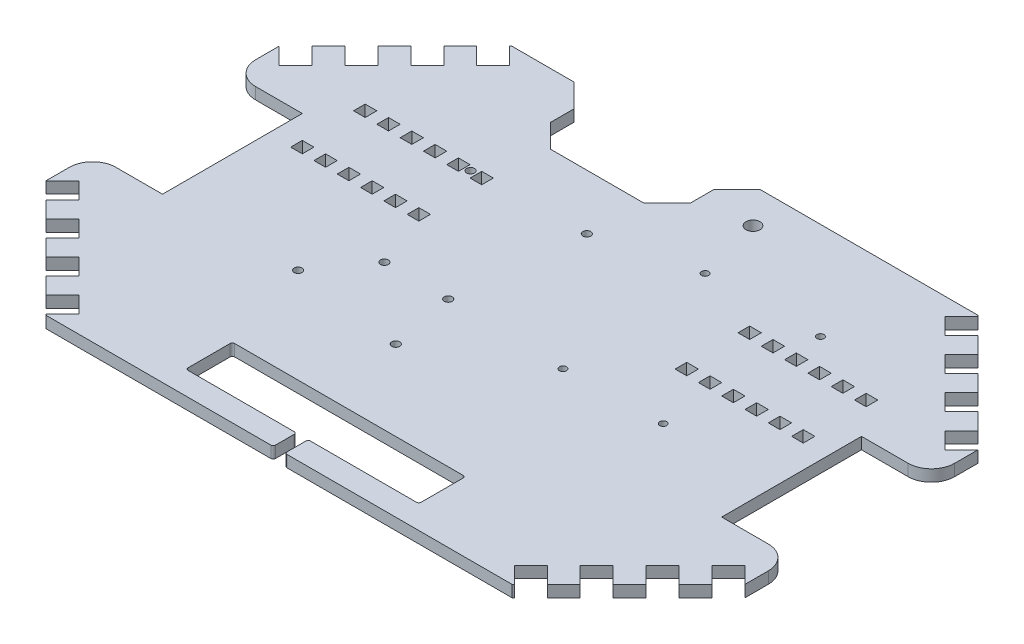
SolidWorks part; units mm, degrees
material "Balsa"
ref_plane "Plan de face" through (0, 0, 0) normal (0, 0, 1) x (1, 0, 0)
ref_plane "Plan de dessus" through (0, 0, 0) normal (0, 1, 0) x (1, 0, 0)
ref_plane "Plan de droite" through (0, 0, 0) normal (1, 0, 0) x (0, 0, -1)
sketch "Esquisse1" plane through (0, 0, 0) normal (0, 1, 0) x (1, 0, 0)
  line L1 (-150, 100) -> (150, 100)
  line L2 (-150, 100) -> (-150, -100)
  line L3 (-150, -100) -> (150, -100)
  line L4 (150, 100) -> (150, -100)
  dimension "D1" = 300
  dimension "D2" = 200
  dimension "D3" = 150
  dimension "D4" = 100
extrude "Boss.-Extru.1" add sketch "Esquisse1" along normal blind 5
sketch "Esquisse2" plane through (0, 5, 0) normal (0, 1, 0) x (1, 0, 0)
  line L0 (-100, 100) -> (-150, 50)
  line L1 (150, 100) -> (-150, 100) construction
  line L2 (-150, 100) -> (-150, -100) construction
  line L3 (-150, 50) -> (-150, 100)
  line L4 (-150, 100) -> (-100, 100)
  line L5 (150, 100) -> (150, 50)
  line L6 (150, -100) -> (150, 100) construction
  line L7 (150, 50) -> (100, 100)
  line L8 (100, 100) -> (150, 100)
  line L9 (150, -100) -> (150, -50)
  line L10 (150, -50) -> (100, -100)
  line L11 (-150, -100) -> (150, -100) construction
  line L12 (100, -100) -> (150, -100)
  line L13 (-100, -100) -> (-150, -100)
  line L14 (-150, -100) -> (-150, -50)
  line L15 (-150, -50) -> (-100, -100)
  dimension "D1" = 50
  dimension "D2" = 50
  dimension "D3" = 50
  dimension "D4" = 50
  dimension "D5" = 50
  dimension "D6" = 50
  dimension "D7" = 50
  dimension "D8" = 50
extrude "Enlèv. mat.-Extru.1" cut sketch "Esquisse2" against normal blind 10
sketch "Esquisse6" plane through (0, 5, 0) normal (0, 1, 0) x (1, 0, 0)
  line L0 (-142.9289, 57.0711) -> (-150, 50)
  line L1 (-142.9289, 57.0711) -> (-135.8579, 50)
  line L2 (-150, 50) -> (-142.9289, 42.9289)
  line L3 (-135.8579, 50) -> (-142.9289, 42.9289)
  line L4 (-150, 50) -> (-100, 100) construction
  dimension "D1" = 10
  dimension "D2" = 10
  dimension "D3" = 0
extrude "Enlèv. mat.-Extru.5" cut sketch "Esquisse6" against normal blind 10
pattern_linear "Répétition linéaire2" count 4 spacing 20 along (0.7071, 0, -0.7071) of "Enlèv. mat.-Extru.5"
mirror "Symétrie1" about plane through (0, 0, 0) normal (0, 0, 1) of "Répétition linéaire2", "Enlèv. mat.-Extru.5"
sketch "Esquisse11" plane through (0, 5, 0) normal (0, 1, 0) x (1, 0, 0)
  line L0 (150, -50) -> (150, 50) construction
  line L1 (150, -7.5) -> (120, -7.5)
  line L2 (150, -7.5) -> (150, 7.5)
  line L3 (150, 7.5) -> (120, 7.5)
  line L4 (120, -7.5) -> (120, 7.5)
  dimension "D1" = 30
  dimension "D2" = 15
  dimension "D3" = 42.5
extrude "Enlèv. mat.-Extru.10" cut sketch "Esquisse11" against normal blind 10
mirror "Symétrie2" about plane through (0, 0, 0) normal (1, 0, 0) of "Enlèv. mat.-Extru.10", "Symétrie1", "Enlèv. mat.-Extru.5", "Répétition linéaire2"
sketch "Esquisse17" plane through (0, 5, 0) normal (0, 1, 0) x (1, 0, 0)
  line L0 (100, 100) -> (-100, 100) construction
  line L1 (-3.4315, 100) -> (-63.4315, 100)
  line L2 (-3.4315, 100) -> (-3.4315, 70)
  line L3 (-3.4315, 70) -> (-63.4315, 70)
  line L4 (-63.4315, 100) -> (-63.4315, 70)
  dimension "D1" = 60
  dimension "D2" = 30
  dimension "D3" = 30
extrude "Enlèv. mat.-Extru.16" cut sketch "Esquisse17" against normal blind 10
chamfer "Chanfrein1" distance 10 angle 45 4 edges at (-63.4315, 2.5, -100) (-63.4315, 2.5, -70) (-3.4315, 2.5, -70) (-3.4315, 2.5, -100)
sketch "Esquisse18" plane through (0, 5, 0) normal (0, 1, 0) x (1, 0, 0)
  line L0 (-150, 50) -> (-150, 7.5) construction
  line L1 (-150, 30) -> (-120, 30)
  line L2 (-150, 30) -> (-150, -30)
  line L3 (-150, -30) -> (-120, -30)
  line L4 (-120, 30) -> (-120, -30)
  line L5 (0, 18.442) -> (0, -22.4339) construction
  line L6 (120, 30) -> (120, -30)
  line L7 (150, -30) -> (120, -30)
  line L8 (150, 30) -> (150, -30)
  line L9 (150, 30) -> (120, 30)
  dimension "D1" = 60
  dimension "D2" = 30
  dimension "D3" = 20
extrude "Enlèv. mat.-Extru.17" cut sketch "Esquisse18" against normal blind 10
sketch "Esquisse20" plane through (0, 0, 0) normal (0, -1, 0) x (1, 0, 0)
  line L0 (-73.4315, -100) -> (-100, -100) construction
  circle A0 centre (18.4315, -85) radius 3
  dimension "D1" = 6
  dimension "D2" = 15
  dimension "D3" = 75
extrude "Enlèv. mat.-Extru.19" cut sketch "Esquisse20" against normal blind 10
sketch "Esquisse21" plane through (0, 0, 0) normal (0, -1, 0) x (1, 0, 0)
  line L1 (110, -42) -> (105, -42)
  line L2 (110, -42) -> (110, -47)
  line L3 (110, -47) -> (105, -47)
  line L4 (105, -42) -> (105, -47)
  line L5 (150, 50) -> (150, 30) construction
  line L6 (95, -42) -> (95, -47)
  line L7 (100, -42) -> (100, -47)
  line L8 (100, -47) -> (95, -47)
  line L9 (100, -42) -> (95, -42)
  line L10 (85, -42) -> (85, -47)
  line L11 (90, -42) -> (90, -47)
  line L12 (90, -47) -> (85, -47)
  line L13 (90, -42) -> (85, -42)
  line L14 (75, -42) -> (75, -47)
  line L15 (80, -42) -> (80, -47)
  line L16 (80, -47) -> (75, -47)
  line L17 (80, -42) -> (75, -42)
  line L18 (65, -42) -> (65, -47)
  line L19 (70, -42) -> (70, -47)
  line L20 (70, -47) -> (65, -47)
  line L21 (70, -42) -> (65, -42)
  line L22 (55, -42) -> (55, -47)
  line L23 (60, -42) -> (60, -47)
  line L24 (60, -47) -> (55, -47)
  line L25 (60, -42) -> (55, -42)
  line L26 (95, -20) -> (100, -20)
  line L27 (105, -20) -> (110, -20)
  line L28 (105, -20) -> (105, -15)
  line L29 (105, -15) -> (110, -15)
  line L30 (110, -20) -> (110, -15)
  line L31 (95, -20) -> (95, -15)
  line L32 (95, -15) -> (100, -15)
  line L33 (100, -20) -> (100, -15)
  line L34 (85, -20) -> (90, -20)
  line L35 (85, -20) -> (85, -15)
  line L36 (85, -15) -> (90, -15)
  line L37 (90, -20) -> (90, -15)
  line L38 (75, -20) -> (80, -20)
  line L39 (75, -20) -> (75, -15)
  line L40 (75, -15) -> (80, -15)
  line L41 (80, -20) -> (80, -15)
  line L42 (65, -20) -> (70, -20)
  line L43 (65, -20) -> (65, -15)
  line L44 (65, -15) -> (70, -15)
  line L45 (70, -20) -> (70, -15)
  line L46 (55, -20) -> (60, -20)
  line L47 (55, -20) -> (55, -15)
  line L48 (55, -15) -> (60, -15)
  line L49 (60, -20) -> (60, -15)
  line L50 (0, -25.8529) -> (0, 42) construction
  line L51 (-60, -20) -> (-60, -15)
  line L52 (-55, -15) -> (-60, -15)
  line L53 (-55, -20) -> (-55, -15)
  line L54 (-55, -20) -> (-60, -20)
  line L55 (-70, -20) -> (-70, -15)
  line L56 (-65, -15) -> (-70, -15)
  line L57 (-65, -20) -> (-65, -15)
  line L58 (-65, -20) -> (-70, -20)
  line L59 (-80, -20) -> (-80, -15)
  line L60 (-75, -15) -> (-80, -15)
  line L61 (-75, -20) -> (-75, -15)
  line L62 (-75, -20) -> (-80, -20)
  line L63 (-90, -20) -> (-90, -15)
  line L64 (-85, -15) -> (-90, -15)
  line L65 (-85, -20) -> (-85, -15)
  line L66 (-85, -20) -> (-90, -20)
  line L67 (-100, -20) -> (-100, -15)
  line L68 (-95, -15) -> (-100, -15)
  line L69 (-95, -20) -> (-95, -15)
  line L70 (-110, -20) -> (-110, -15)
  line L71 (-105, -15) -> (-110, -15)
  line L72 (-105, -20) -> (-105, -15)
  line L73 (-105, -20) -> (-110, -20)
  line L74 (-95, -20) -> (-100, -20)
  line L75 (-60, -42) -> (-55, -42)
  line L76 (-60, -47) -> (-55, -47)
  line L77 (-60, -42) -> (-60, -47)
  line L78 (-55, -42) -> (-55, -47)
  line L79 (-70, -42) -> (-65, -42)
  line L80 (-70, -47) -> (-65, -47)
  line L81 (-70, -42) -> (-70, -47)
  line L82 (-65, -42) -> (-65, -47)
  line L83 (-80, -42) -> (-75, -42)
  line L84 (-80, -47) -> (-75, -47)
  line L85 (-80, -42) -> (-80, -47)
  line L86 (-75, -42) -> (-75, -47)
  line L87 (-90, -42) -> (-85, -42)
  line L88 (-90, -47) -> (-85, -47)
  line L89 (-90, -42) -> (-90, -47)
  line L90 (-85, -42) -> (-85, -47)
  line L91 (-100, -42) -> (-95, -42)
  line L92 (-100, -47) -> (-95, -47)
  line L93 (-100, -42) -> (-100, -47)
  line L94 (-95, -42) -> (-95, -47)
  line L95 (-105, -42) -> (-105, -47)
  line L96 (-110, -47) -> (-105, -47)
  line L97 (-110, -42) -> (-110, -47)
  line L98 (-110, -42) -> (-105, -42)
  line L99 (100, -100) -> (6.5685, -100) construction
  dimension "D1" = 5
  dimension "D2" = 5
  dimension "D3" = 53
  dimension "D4" = 40
  dimension "D6" = 5
  dimension "D7" = 5
  dimension "D8" = 22
  dimension "D5" = 6
  dimension "D9" = 6
extrude "Enlèv. mat.-Extru.20" cut sketch "Esquisse21" against normal blind 10
sketch "Esquisse22" plane through (0, 0, 0) normal (0, -1, 0) x (1, 0, 0)
  line L0 (-100, 100) -> (100, 100) construction
  line L1 (50, 90) -> (-50, 90)
  line L2 (50, 90) -> (50, 70)
  line L3 (50, 70) -> (-50, 70)
  line L4 (-50, 90) -> (-50, 70)
  line L6 (2.5, 90) -> (-2.5, 90)
  line L7 (2.5, 90) -> (2.5, 100)
  line L8 (2.5, 100) -> (-2.5, 100)
  line L9 (-2.5, 90) -> (-2.5, 100)
  dimension "D1" = 100
  dimension "D2" = 20
  dimension "D3" = 50
  dimension "D4" = 10
  dimension "D5" = 97.5
  dimension "D6" = 97.5
extrude "Enlèv. mat.-Extru.21" cut sketch "Esquisse22" against normal blind 10 contours L1 L4 L3 L2 | L9 L1 L7 L8
fillet "Congé1" radius 1 8 edges at (-50, 2.5, 90) (-50, 2.5, 70) (-2.5, 2.5, 100) (2.5, 2.5, 100) (-2.5, 2.5, 90) (2.5, 2.5, 90) (50, 2.5, 90) (50, 2.5, 70)
sketch "Esquisse23" plane through (0, 0, 0) normal (0, -1, 0) x (1, 0, 0)
  line L0 (-82, -57) -> (-82, 45)
  line L1 (-82, -57) -> (-28, -57)
  line L2 (-28, -57) -> (-28, 45)
  line L3 (-82, 45) -> (-28, 45)
  line L4 (-120, -30) -> (-120, 30) construction
  line L5 (-100, 100) -> (-3.5, 100) construction
  circle A0 centre (-30.5, -45) radius 1.5
  circle A1 centre (-30.5, 30) radius 1.5
  circle A2 centre (-79, -52) radius 1.5
  circle A3 centre (-79, 31) radius 1.5
  circle A4 centre (-79, -52) radius 1.5
  circle A5 centre (-30.5, -45) radius 1.5
  circle A6 centre (-79, 31) radius 1.5
  circle A7 centre (-30.5, 30) radius 1.5
  circle A8 centre (72.7099, 7.8179) radius 1.5
  circle A9 centre (30.8151, 8.9467) radius 1.5
  circle A10 centre (25.8625, -56.9838) radius 1.5
  circle A11 centre (74.105, -58.2837) radius 1.5
  dimension "D2" = 3
  dimension "D3" = 3
  dimension "D5" = 3
  dimension "D6" = 3
  dimension "D15" = 38
  dimension "D16" = 55
  dimension "D17" = 3
  dimension "D18" = 3
  dimension "D19" = 3
  dimension "D20" = 3
  dimension "D1" = 102
  dimension "D4" = 54
  dimension "D7" = 15
  dimension "D8" = 14
  dimension "D9" = 5
  dimension "D10" = 12
  dimension "D11" = 3
  dimension "D12" = 3
  dimension "D13" = 2.5
  dimension "D14" = 2.5
extrude "Enlèv. mat.-Extru.23" cut sketch "Esquisse23" against normal blind 10 contours A9 | A8 | A10 | A11
sketch "Esquisse24" plane through (0, 0, 0) normal (0, -1, 0) x (-1, 0, 0)
  circle A0 centre (62.6177, -29.1624) radius 1.7
  circle A1 centre (62.6177, 44.8376) radius 1.7
  circle A2 centre (14.2177, 46.3376) radius 1.7
  circle A3 centre (14.2177, -35.6624) radius 1.7
  circle A4 centre (47.1177, -7.6624) radius 1.7
  circle A5 centre (19.7177, -7.6624) radius 1.7
extrude "Enlèv. mat.-Extru.24" cut sketch "Esquisse24" against normal blind 10
fillet "Congé2" radius 10 4 edges at (150, 2.5, 30) (150, 2.5, -30) (-150, 2.5, -30) (-150, 2.5, 30)
